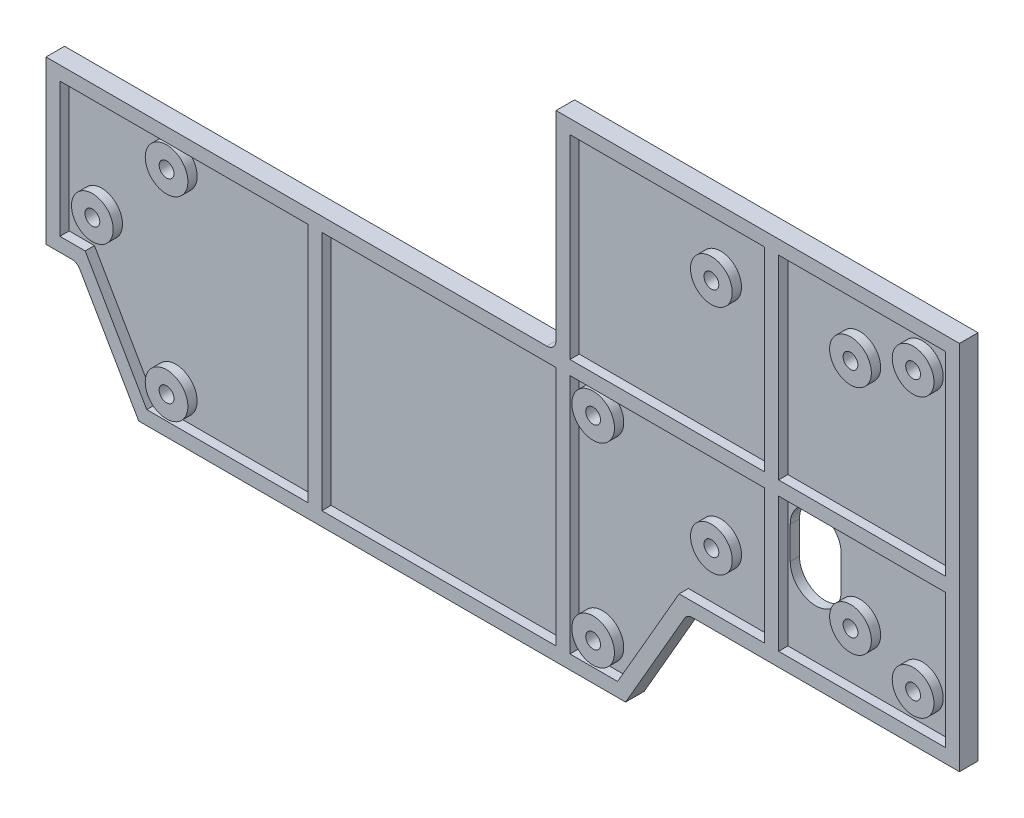
SolidWorks part; units mm, degrees
ref_plane "Plan de face" through (0, 0, 0) normal (0, 0, 1) x (1, 0, 0)
ref_plane "Plan de dessus" through (0, 0, 0) normal (0, 1, 0) x (1, 0, 0)
ref_plane "Plan de droite" through (0, 0, 0) normal (1, 0, 0) x (0, 0, -1)
sketch "Esquisse1" plane through (0, 0, 0) normal (0, 0, 1) x (1, 0, 0)
  line L0 (0, 0) -> (60, 0) construction
  line L1 (88.5, 30) -> (-88.5, 30) construction
  line L2 (88.5, 30) -> (88.5, -30) construction
  line L3 (88.5, -30) -> (-88.5, -30) construction
  line L4 (-88.5, 30) -> (-88.5, -30) construction
  line L5 (88.5, 30) -> (-88.5, -30) construction
  line L6 (88.5, -30) -> (-88.5, 30) construction
  line L7 (75, 25) -> (45, 25) construction
  line L8 (75, 25) -> (75, -25) construction
  line L9 (75, -25) -> (45, -25) construction
  line L10 (45, 25) -> (45, -25) construction
  line L11 (75, 25) -> (45, -25) construction
  line L12 (75, -25) -> (45, 25) construction
  line L14 (98.5, 40) -> (-98.5, 40)
  line L15 (98.5, 40) -> (98.5, -40)
  line L16 (98.5, -40) -> (-98.5, -40)
  line L17 (-98.5, 40) -> (-98.5, -40)
  line L18 (98.5, 40) -> (-98.5, -40) construction
  line L19 (98.5, -40) -> (-98.5, 40) construction
  circle A0 centre (-88.5, -30) radius 1.6
  circle A1 centre (88.5, 30) radius 1.6
  circle A2 centre (88.5, -30) radius 1.6
  circle A3 centre (-88.5, 30) radius 1.6
  circle A4 centre (45, 25) radius 1.6
  circle A5 centre (75, 25) radius 1.6
  circle A6 centre (45, -25) radius 1.6
  circle A7 centre (75, -25) radius 1.6
  point P0 (0, 0)
  point P10 (60, 0)
  dimension "D1" = 3.2
  dimension "D2" = 3.2
  dimension "D3" = 3.2
  dimension "D4" = 3.2
  dimension "D10" = 3.2
  dimension "D11" = 3.2
  dimension "D12" = 3.2
  dimension "D13" = 3.2
  dimension "D5" = 177
  dimension "D6" = 60
  dimension "D7" = 30
  dimension "D8" = 50
  dimension "D9" = 60
  dimension "D14" = 10
  dimension "D15" = 10
extrude "Boss.-Extru.1" add sketch "Esquisse1" along normal blind 2
sketch "Esquisse2" plane through (0, 0, 2) normal (0, 0, 1) x (1, 0, 0)
  line L1 (-98.5, 40) -> (11.5, 40)
  line L2 (-98.5, 40) -> (-98.5, -5)
  line L3 (-98.5, -5) -> (11.5, -5)
  line L4 (11.5, 40) -> (11.5, -5)
  dimension "D1" = 45
  dimension "D2" = 110
extrude "Enlèv. mat.-Extru.1" cut sketch "Esquisse2" against normal blind 2
sketch "Esquisse8" plane through (0, 0, 2) normal (0, 0, 1) x (1, 0, 0)
  line L0 (-91.7791, -40) -> (-78.5, -63)
  line L1 (-98.5, -40) -> (98.5, -40) construction
  line L2 (-78.5, -63) -> (26.5, -63)
  line L3 (26.5, -63) -> (39.7791, -40)
  line L4 (-98.5, -5) -> (11.5, -5) construction
  line L5 (-98.5, -5) -> (-98.5, -40) construction
  line L6 (-91.7791, -40) -> (39.7791, -40)
  dimension "D1" = 58
  dimension "D2" = 105
  dimension "D3" = 20
  dimension "D4" = 60
  dimension "D5" = 60
extrude "Boss.-Extru.6" add sketch "Esquisse8" against normal blind 2
sketch "Esquisse3" plane through (0, 0, 2) normal (0, 0, 1) x (1, 0, 0)
  line L6 (98.5, 40) -> (11.5, 40)
  line L7 (11.5, 40) -> (11.5, -5)
  line L8 (11.5, -5) -> (-98.5, -5)
  line L9 (-98.5, -5) -> (-98.5, -40)
  line L10 (-98.5, -40) -> (-91.7791, -40)
  line L11 (98.5, -40) -> (98.5, 40)
  line L12 (98.5, 40) -> (11.5, 40)
  line L13 (11.5, 40) -> (11.5, -5)
  line L14 (11.5, -5) -> (-98.5, -5)
  line L15 (-98.5, -5) -> (-98.5, -40)
  line L16 (-98.5, -40) -> (-91.7791, -40)
  line L17 (98.5, -40) -> (98.5, 40)
  line L22 (-91.7791, -40) -> (-78.5, -63)
  line L23 (-91.7791, -40) -> (-78.5, -63)
  line L24 (95.5, 37) -> (14.5, 37)
  line L25 (14.5, 37) -> (14.5, -8)
  line L26 (14.5, -8) -> (-95.5, -8)
  line L27 (-95.5, -8) -> (-95.5, -37)
  line L28 (-95.5, -37) -> (-90.047, -37)
  line L29 (95.5, -37) -> (95.5, 37)
  line L30 (95.5, 37) -> (14.5, 37)
  line L31 (14.5, 37) -> (14.5, -8)
  line L32 (14.5, -8) -> (-95.5, -8)
  line L33 (-95.5, -8) -> (-95.5, -37)
  line L34 (-95.5, -37) -> (-90.047, -37)
  line L35 (95.5, -37) -> (95.5, 37)
  line L36 (-78.5, -63) -> (26.5, -63)
  line L37 (-78.5, -63) -> (26.5, -63)
  line L38 (26.5, -63) -> (39.7791, -40)
  line L39 (26.5, -63) -> (39.7791, -40)
  line L40 (39.7791, -40) -> (98.5, -40)
  line L41 (39.7791, -40) -> (98.5, -40)
  line L42 (-90.047, -37) -> (-76.7679, -60)
  line L43 (-90.047, -37) -> (-76.7679, -60)
  line L44 (-76.7679, -60) -> (24.7679, -60)
  line L45 (-76.7679, -60) -> (24.7679, -60)
  line L46 (24.7679, -60) -> (38.047, -37)
  line L47 (24.7679, -60) -> (38.047, -37)
  line L48 (38.047, -37) -> (95.5, -37)
  line L49 (38.047, -37) -> (95.5, -37)
  dimension "D1" = 0
  dimension "D2" = 3
extrude "Boss.-Extru.2" add sketch "Esquisse3" along normal blind 2
sketch "Esquisse4" plane through (0, 0, 2) normal (0, 0, 1) x (1, 0, 0)
  line L1 (14.5, -5) -> (11.5, -5)
  line L2 (11.5, -5) -> (11.5, -60)
  line L3 (11.5, -60) -> (14.5, -60)
  line L5 (14.5, 37) -> (14.5, -8) construction
  line L7 (14.5, -5) -> (98.5, -5)
  line L9 (14.5, -8) -> (98.5, -8)
  line L10 (98.5, -5) -> (98.5, -8)
  line L11 (98.5, -40) -> (98.5, 40) construction
  line L12 (4.5, -6.5) -> (98.5, -6.5) construction
  line L13 (-76.7679, -60) -> (24.7679, -60) construction
  line L14 (-40.5, -8) -> (-40.5, -60) construction
  line L15 (14.5, -8) -> (-95.5, -8) construction
  line L16 (14.5, -8) -> (-95.5, -8) construction
  line L17 (-39, -60) -> (-42, -60)
  line L18 (-39, -60) -> (-39, -8)
  line L19 (-39, -8) -> (-42, -8)
  line L20 (-42, -60) -> (-42, -8)
  line L21 (-39, -60) -> (-42, -8) construction
  line L22 (-39, -8) -> (-42, -60) construction
  line L23 (14.5, -8) -> (14.5, -60)
  point P3 (4.5, -8)
  point P7 (4.5, -52)
  point P14 (-42, -8)
  point P24 (-40.5, -34)
  dimension "D2" = 3
extrude "Boss.-Extru.3" add sketch "Esquisse4" along normal blind 2
sketch "Esquisse5" plane through (0, 0, 2) normal (0, 0, 1) x (1, 0, 0)
  line L0 (58, 37) -> (58, -37) construction
  line L1 (95.5, 37) -> (14.5, 37) construction
  line L2 (-95.5, -37) -> (-90.047, -37) construction
  line L4 (59.5, -37) -> (56.5, -37)
  line L5 (59.5, -37) -> (59.5, 37)
  line L6 (59.5, 37) -> (56.5, 37)
  line L7 (56.5, -37) -> (56.5, 37)
  line L8 (59.5, -37) -> (56.5, 37) construction
  line L9 (59.5, 37) -> (56.5, -37) construction
  point P6 (58, 0)
  dimension "D1" = 3
  dimension "D2" = 58
extrude "Boss.-Extru.4" add sketch "Esquisse5" along normal blind 2
sketch "Esquisse6" plane through (0, 0, 2) normal (0, 0, 1) x (1, 0, 0)
  circle A0 centre (-88.5, -30) radius 1.6 construction
  circle A1 centre (-88.5, -30) radius 1.6
  circle A2 centre (-88.5, -30) radius 4.5
  circle A3 centre (88.5, -30) radius 4.5
  circle A4 centre (75, -25) radius 4.5
  circle A5 centre (45, -25) radius 4.5
  circle A6 centre (45, 25) radius 4.5
  circle A7 centre (75, 25) radius 4.5
  circle A8 centre (88.5, 30) radius 4.5
  circle A9 centre (45, -25) radius 1.6 construction
  circle A10 centre (45, -25) radius 1.6
  circle A11 centre (45, 25) radius 1.6 construction
  circle A12 centre (45, 25) radius 1.6
  circle A13 centre (75, 25) radius 1.6 construction
  circle A14 centre (75, 25) radius 1.6
  circle A15 centre (88.5, 30) radius 1.6 construction
  circle A16 centre (88.5, 30) radius 1.6
  circle A17 centre (88.5, -30) radius 1.6 construction
  circle A18 centre (88.5, -30) radius 1.6
  circle A19 centre (75, -25) radius 1.6 construction
  circle A20 centre (75, -25) radius 1.6
  dimension "D1" = 9
  dimension "D2" = 9
  dimension "D3" = 9
  dimension "D4" = 9
  dimension "D5" = 9
  dimension "D6" = 9
  dimension "D7" = 9
extrude "Boss.-Extru.5" add sketch "Esquisse6" along normal blind 2
sketch "Esquisse7" plane through (0, 0, 2) normal (0, 0, 1) x (1, 0, 0)
  line L0 (65.5, -14) -> (65.5, -21) construction
  line L1 (71, -14) -> (71, -21)
  line L2 (60, -14) -> (60, -21)
  line L3 (59.5, -37) -> (59.5, -8) construction
  line L4 (59.5, -8) -> (95.5, -8) construction
  line L5 (-95.5, -37) -> (-90.047, -37) construction
  arc A0 (71, -14) -> (60, -14) centre (65.5, -14) ccw
  arc A1 (60, -21) -> (71, -21) centre (65.5, -21) ccw
  point P2 (65.5, -17.5)
  dimension "D1" = 11
  dimension "D2" = 6
  dimension "D3" = 6
  dimension "D4" = 16
extrude "Enlèv. mat.-Extru.2" cut sketch "Esquisse7" against normal blind 10
sketch "Esquisse9" plane through (0, 0, 0) normal (0, 0, -1) x (-1, 0, 0)
  line L1 (76.5, -59) -> (-23.5, -59) construction
  line L2 (76.5, -59) -> (76.5, -9) construction
  line L3 (76.5, -9) -> (-23.5, -9) construction
  line L4 (-23.5, -59) -> (-23.5, -9) construction
  line L5 (76.5, -59) -> (-23.5, -9) construction
  line L6 (76.5, -9) -> (-23.5, -59) construction
  line L7 (72.5, -13) -> (-19.5, -13) construction
  line L8 (72.5, -13) -> (72.5, -55) construction
  line L9 (72.5, -55) -> (-19.5, -55) construction
  line L10 (-19.5, -13) -> (-19.5, -55) construction
  line L11 (72.5, -13) -> (-19.5, -55) construction
  line L12 (72.5, -55) -> (-19.5, -13) construction
  line L13 (78.5, -63) -> (-26.5, -63) construction
  line L14 (98.5, -5) -> (98.5, -40) construction
  circle A0 centre (-19.5, -13) radius 1.6
  circle A1 centre (-19.5, -55) radius 1.6
  circle A2 centre (72.5, -13) radius 1.6
  circle A3 centre (72.5, -55) radius 1.6
  point P0 (26.5, -34)
  point P8 (26.5, -34)
  point P15 (0, 0)
  point P16 (72.9467, -56.4682)
  dimension "D5" = 3.2
  dimension "D6" = 3.2
  dimension "D7" = 3.2
  dimension "D8" = 3.2
  dimension "D1" = 50
  dimension "D2" = 100
  dimension "D3" = 4
  dimension "D4" = 4
  dimension "D9" = 29
  dimension "D10" = 72
extrude "Enlèv. mat.-Extru.3" cut sketch "Esquisse9" against normal blind 2
sketch "Esquisse10" plane through (0, 0, 2) normal (0, 0, 1) x (1, 0, 0)
  circle A0 centre (-72.5, -13) radius 1.6 construction
  circle A1 centre (-72.5, -13) radius 1.6
  circle A2 centre (-72.5, -55) radius 1.6 construction
  circle A3 centre (-72.5, -55) radius 1.6
  circle A4 centre (19.5, -13) radius 1.6 construction
  circle A5 centre (19.5, -13) radius 1.6
  circle A6 centre (19.5, -55) radius 1.6 construction
  circle A7 centre (19.5, -55) radius 1.6
  circle A8 centre (-72.5, -13) radius 4.6
  circle A9 centre (-72.5, -55) radius 4.6
  circle A10 centre (19.5, -13) radius 4.6
  circle A11 centre (19.5, -55) radius 4.6
  dimension "D1" = 3
extrude "Boss.-Extru.7" add sketch "Esquisse10" along normal blind 2
fillet "Congé14" radius 2 3 edges at (11.5, -5, 2) (39.7791, -40, 2) (-91.7791, -40, 2)
